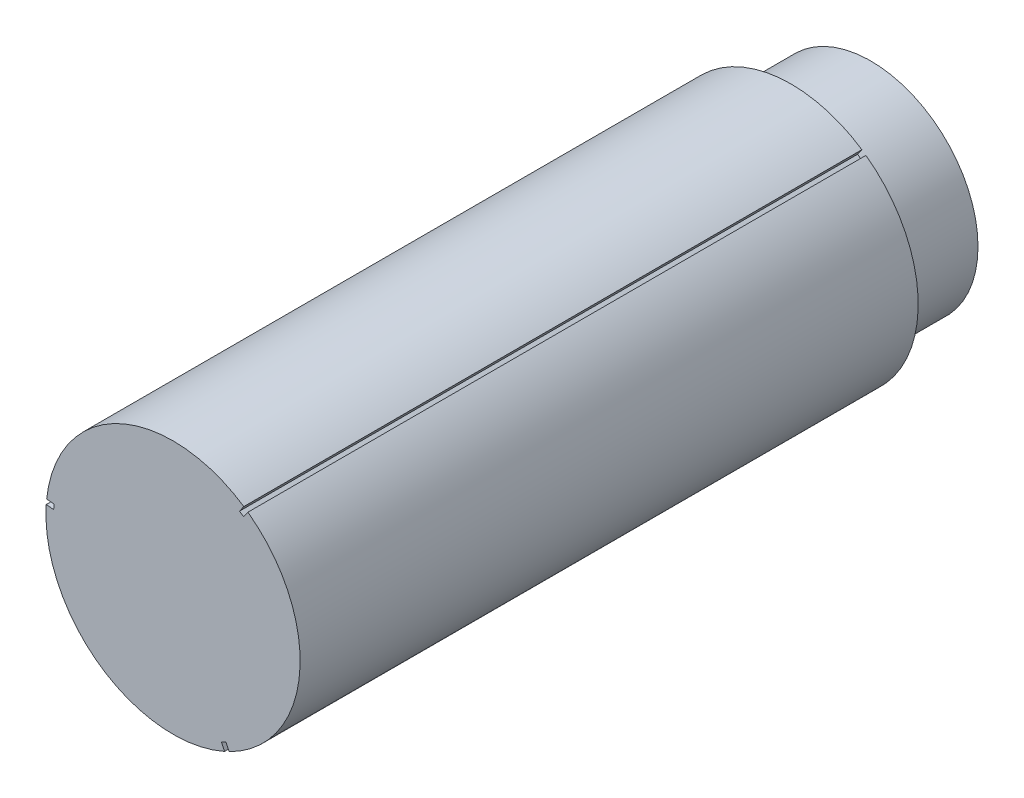
SolidWorks part; units mm, degrees
ref_plane "Face" through (0, 0, 0) normal (0, 0, 1) x (1, 0, 0)
ref_plane "Droite" through (0, 0, 0) normal (0, 1, 0) x (1, 0, 0)
ref_plane "Dessus" through (0, 0, 0) normal (1, 0, 0) x (0, 0, -1)
sketch "Esquisse1" plane through (0, 0, 0) normal (0, 0, 1) x (1, 0, 0)
  circle A0 centre (0, 0) radius 10.75
  circle A1 centre (0, 0) radius 2.75
  dimension "D1" = 21.5
  dimension "D2" = 5.5
extrude "Base-Extrusion" add sketch "Esquisse1" along normal blind 8
sketch "Esquisse2" plane through (0, 0, 8) normal (0, 0, 1) x (1, 0, 0)
  circle A0 centre (0, 0) radius 12.75
  dimension "D1" = 25.5
extrude "Boss.-Extru.1" add sketch "Esquisse2" along normal blind 62
sketch "Esquisse4" plane through (0, 0, 70) normal (0, 0, 1) x (1, 0, 0)
  line L0 (0, 0) -> (14.8044, 0) construction
  line L1 (0, 0) -> (0, 13.6348) construction
  line L2 (8.2683, 11.8227) -> (0, 0) construction
  line L3 (0, 0) -> (5.7447, -12.301) construction
  line L4 (-13.1564, 1.1434) -> (0, 0) construction
  line L6 (7.1008, 10.5896) -> (6.6724, 9.977)
  line L7 (6.6724, 9.977) -> (7.0822, 9.6905)
  line L8 (7.0822, 9.6905) -> (7.5106, 10.3031)
  line L15 (5.6205, -11.4443) -> (5.3042, -10.767)
  line L16 (5.3042, -10.767) -> (4.8511, -10.9786)
  line L17 (4.8511, -10.9786) -> (5.1674, -11.6559)
  line L21 (-12.7213, 0.8547) -> (-11.9766, 0.79)
  line L22 (-11.9766, 0.79) -> (-11.9333, 1.2881)
  line L23 (-11.9333, 1.2881) -> (-12.678, 1.3528)
  circle A0 centre (0, 0) radius 12.75 construction
  arc A1 (7.5106, 10.3031) -> (7.1008, 10.5896) centre (0, 0) ccw
  arc A2 (-12.678, 1.3528) -> (-12.7213, 0.8547) centre (0, 0) ccw
  arc A3 (5.1674, -11.6559) -> (5.6205, -11.4443) centre (0, 0) ccw
  dimension "D4" = 0.7475
  dimension "D5" = 0.5
  dimension "D6" = 0.5
  dimension "D7" = 12
  dimension "D1" = 55.033
  dimension "D8" = 64.967
  dimension "D2" = 12.0026
  dimension "D9" = 120
  dimension "D3" = 0.5
  dimension "D10" = 12
extrude "Enlèv. mat.-Extru.1" cut sketch "Esquisse4" against normal up to next
